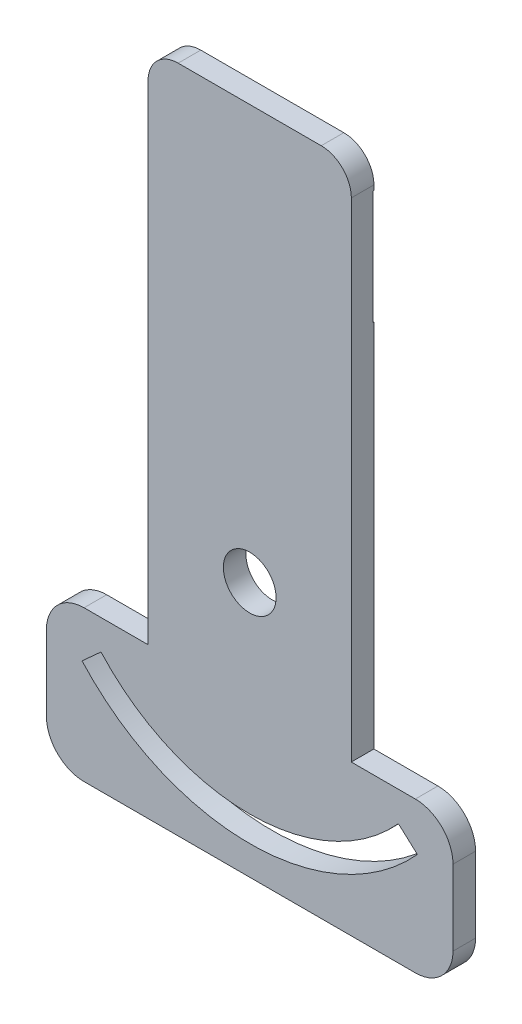
SolidWorks part; units mm, degrees
ref_plane "Alzado" through (0, 0, 0) normal (0, 0, 1) x (1, 0, 0)
ref_plane "Planta" through (0, 0, 0) normal (0, 1, 0) x (1, 0, 0)
ref_plane "Vista lateral" through (0, 0, 0) normal (1, 0, 0) x (0, 0, -1)
sketch "Corte exterior" plane through (0, 0, 0) normal (0, 0, 1) x (1, 0, 0)
  line L0 (19.522, -6.0858) -> (11.022, -6.0858)
  line L1 (46.5148, -6.0858) -> (55.022, -6.0858)
  line L2 (11.022, -26.0858) -> (55.022, -26.0858)
  line L3 (42.522, 62.812) -> (23.522, 62.812)
  line L4 (46.5148, -6.0858) -> (46.522, 58.812)
  line L5 (55.2949, -12.3304) -> (52.7732, -10.0498)
  line L6 (13.2708, -10.0498) -> (10.749, -12.3304)
  line L7 (60.0153, -11.0858) -> (60.0153, -21.0858)
  line L8 (60.022, -11.0858) -> (60.022, -21.0858)
  line L9 (6.022, -11.0858) -> (6.022, -21.0858)
  line L10 (19.522, 58.812) -> (19.522, -6.0858)
  arc A0 (23.522, 62.812) -> (19.522, 58.812) centre (23.522, 58.812) ccw
  arc A1 (46.522, 58.812) -> (42.522, 62.812) centre (42.522, 58.812) ccw
  circle A2 centre (33.022, 7.812) radius 3.5
  arc A3 (6.022, -21.0858) -> (11.022, -26.0858) centre (11.022, -21.0858) ccw
  arc A4 (55.022, -26.0858) -> (60.022, -21.0858) centre (55.022, -21.0858) ccw
  arc A5 (60.022, -11.0858) -> (55.022, -6.0858) centre (55.022, -11.0858) ccw
  arc A6 (11.022, -6.0858) -> (6.022, -11.0858) centre (11.022, -11.0858) ccw
  arc A7 (10.749, -12.3304) -> (55.2949, -12.3304) centre (33.022, 7.812) ccw
  arc A8 (13.2708, -10.0498) -> (52.7732, -10.0498) centre (33.022, 7.812) ccw
sketch "Grabado Superficie" plane through (0, 0, 0) normal (0, 0, 1) x (1, 0, 0)
  line L0 (35.8913, 9.8162) -> (35.017, 22.2029)
  line L1 (31.027, 22.2029) -> (30.1526, 9.8162)
  arc A0 (35.017, 22.2029) -> (31.027, 22.2029) centre (33.022, 22.062) ccw
  arc A1 (35.8913, 9.8162) -> (30.1526, 9.8162) centre (33.022, 7.812) ccw
sketch "grabado linea medio" plane through (0, 0, 0) normal (0, 0, 1) x (1, 0, 0)
  line L0 (42.4601, 43.0172) -> (46.5401, 43.0151)
  line L1 (42.456, 34.9372) -> (42.4601, 43.0172)
  line L2 (38.396, 34.9393) -> (42.456, 34.9372)
  line L3 (38.3936, 30.2993) -> (38.396, 34.9393)
  line L4 (35.8736, 30.3006) -> (38.3936, 30.2993)
  line L5 (35.876, 34.9406) -> (35.8736, 30.3006)
  line L6 (19.536, 34.949) -> (35.876, 34.9406)
  line L7 (35.8879, 58.1694) -> (19.5478, 57.9778)
  line L8 (35.8903, 62.8106) -> (35.8879, 58.1694)
  line L9 (38.4079, 58.1693) -> (38.4103, 62.8093)
  line L10 (46.5479, 58.1651) -> (38.4079, 58.1693)
  line L11 (46.5401, 43.0151) -> (46.5479, 58.1651)
  line L12 (19.536, 34.949) -> (19.5478, 57.9778)
  line L13 (38.4103, 62.8093) -> (35.8903, 62.8106)
extrude "Saliente-Extruir1" add sketch "Corte exterior" along normal blind 3
extrude "Cortar-Extruir1" cut sketch "Grabado Superficie" along normal blind 1
extrude "Cortar-Extruir2" cut sketch "grabado linea medio" along normal blind 0.1
